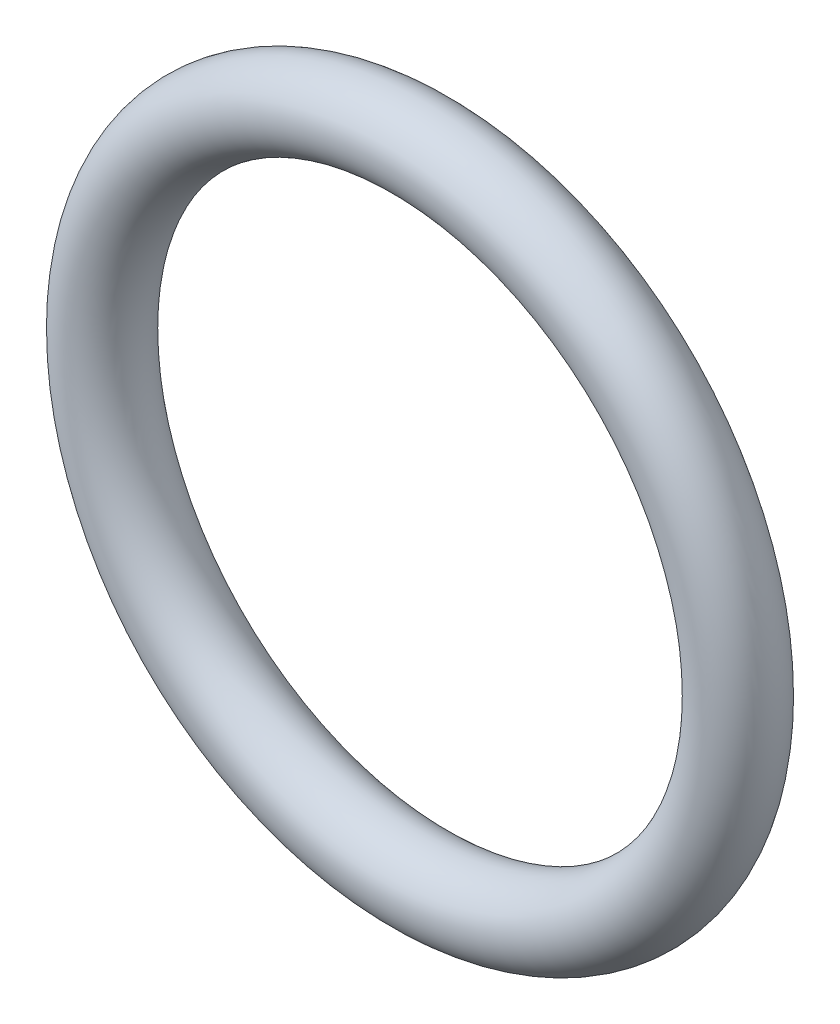
SolidWorks part; units mm, degrees
material "Rubber"
ref_plane "Front Plane" through (0, 0, 0) normal (0, 0, 1) x (1, 0, 0)
ref_plane "Top Plane" through (0, 0, 0) normal (0, 1, 0) x (1, 0, 0)
ref_plane "Right Plane" through (0, 0, 0) normal (1, 0, 0) x (0, 0, -1)
sketch "Sketch1" plane through (0, 0, 0) normal (1, 0, 0) x (0, 0, -1)
  line L0 (-10.8826, 0) -> (10.4327, 0) construction
  circle A0 centre (0, 14.2621) radius 1.7653
  point P2 (0, 12.4968)
  point P3 (0, 16.0274)
  dimension "D1" = 32.0548
  dimension "D2" = 24.9936
revolve "Revolve2" add sketch "Sketch1" angle 360 about L0
